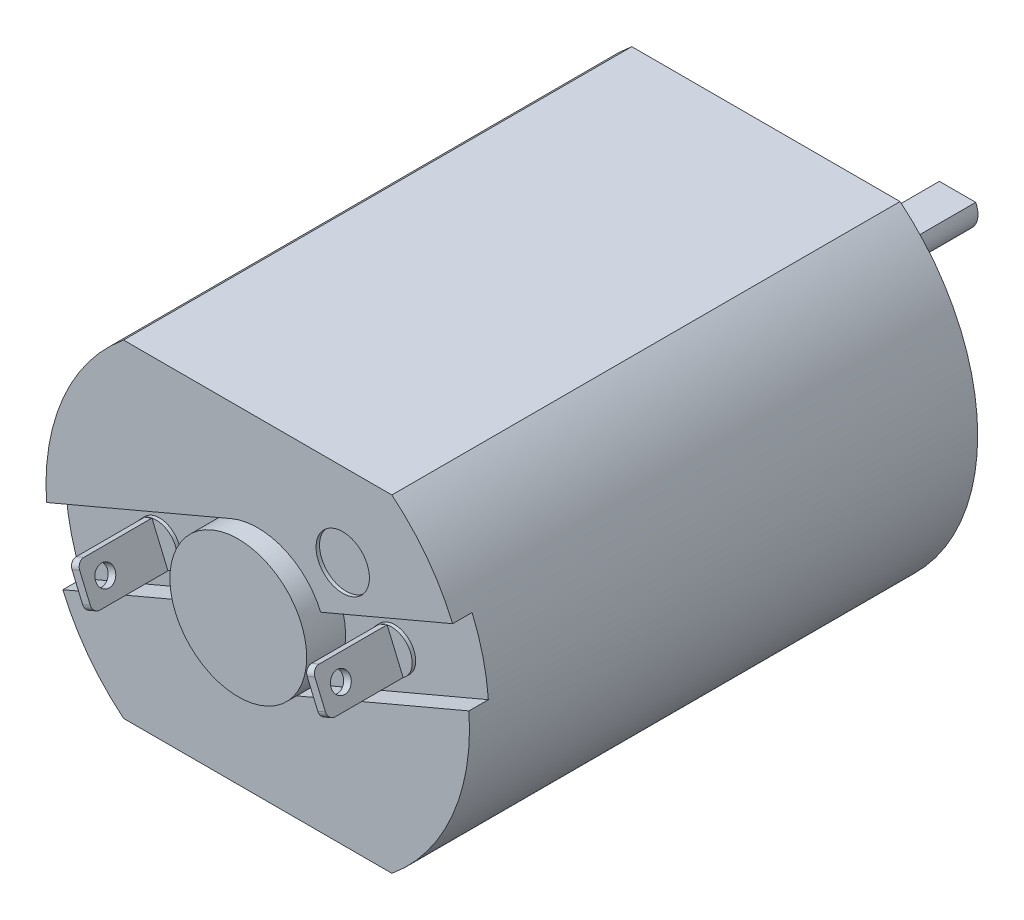
SolidWorks part; units mm, degrees
ref_plane "Front" through (0, 0, 0) normal (0, 0, 1) x (1, 0, 0)
ref_plane "Top" through (0, 0, 0) normal (0, 1, 0) x (1, 0, 0)
ref_plane "Right" through (0, 0, 0) normal (1, 0, 0) x (0, 0, -1)
sketch "Sketch1" plane through (0, 0, 0) normal (0, 0, 1) x (1, 0, 0)
  line L0 (-4.9075, 5.9944) -> (4.9075, 5.9944)
  line L1 (-4.9075, -5.9944) -> (4.9075, -5.9944)
  arc A0 (-4.9075, 5.9944) -> (-4.9075, -5.9944) centre (0, 0) ccw
  arc A1 (4.9075, -5.9944) -> (4.9075, 5.9944) centre (0, 0) ccw
  dimension "D1" = 15.494
  dimension "D2" = 5.9944
  dimension "D3" = 11.9888
extrude "Extrude1" add sketch "Sketch1" along normal blind 18.5928
sketch "Sketch2" plane through (0, 0, 0) normal (0, 0, -1) x (-1, 0, 0)
  circle A0 centre (0, 0) radius 2.3495
  dimension "D1" = 4.699
extrude "Extrude2" add sketch "Sketch2" along normal blind 1.524
sketch "Sketch3" plane through (0, 0, -1.524) normal (0, 0, -1) x (-1, 0, 0)
  circle A0 centre (0, 0) radius 0.748
  dimension "D1" = 1.4961
extrude "Extrude3" add sketch "Sketch3" along normal blind 5.4864
sketch "Sketch4" plane through (0, 0, 18.5928) normal (0, 0, 1) x (1, 0, 0)
  circle A0 centre (0, 0) radius 2.5019
  dimension "D1" = 5.0038
extrude "Extrude4" add sketch "Sketch4" along normal blind 0.7112
sketch "Sketch6" plane through (0, 0, 0) normal (0, 0, -1) x (-1, 0, 0)
  line L0 (0, 0) -> (-5.4518, -3.1476) construction
  line L1 (0, 0) -> (6.0345, 3.484) construction
  line L2 (0, 0) -> (6.2404, 0) construction
  line L3 (0, 0) -> (-6.1628, 0) construction
  circle A0 centre (0, 0) radius 2.3495 construction
  circle A1 centre (4.3334, 2.5019) radius 0.8066
  circle A2 centre (0, 0) radius 5.0038 construction
  circle A3 centre (-4.3334, -2.5019) radius 0.8001
  dimension "D1" = 1.6132
  dimension "D2" = 1.6002
  dimension "D7" = 10.0076
  dimension "D5" = 30
  dimension "D6" = 30
extrude "Cut-Extrude1" cut sketch "Sketch6" against normal blind 2
sketch "Sketch8" plane through (0, 0, 18.5928) normal (0, 0, 1) x (1, 0, 0)
  line L0 (2.303, 0.9776) -> (7.2224, 3.0657)
  line L1 (8.2, 0.7627) -> (0.9776, -2.303)
  line L3 (7.2224, 3.0657) -> (8.2, 0.7627)
  line L4 (0, 0) -> (4.7854, 0) construction
  circle A0 centre (0, 0) radius 2.5019 construction
  arc A3 (0.9776, -2.303) -> (2.303, 0.9776) centre (0, 0) ccw
  dimension "D1" = 23
  dimension "D2" = 7.8462
extrude "Cut-Extrude2" cut sketch "Sketch8" against normal blind 0.7112
sketch "Sketch9" plane through (0, 0, 18.5928) normal (0, 0, 1) x (1, 0, 0)
  line L0 (-2.303, -0.9776) -> (-8.4179, -3.5732)
  line L1 (-8.4179, -3.5732) -> (-9.3954, -1.2702)
  line L2 (-9.3954, -1.2702) -> (-0.9776, 2.303)
  line L5 (0.9776, -2.303) -> (7.7266, 0.5618) construction
  circle A0 centre (0, 0) radius 2.5019 construction
  arc A1 (-0.9776, 2.303) -> (-2.303, -0.9776) centre (0, 0) ccw
  dimension "D1" = 9.1448
extrude "Cut-Extrude3" cut sketch "Sketch9" against normal blind 0.7112
sketch "Sketch10" plane through (0, 0, 17.8816) normal (0, 0, 1) x (1, 0, 0)
  line L0 (-4.7354, 0.1698) -> (-4.1499, -1.2096)
  line L1 (-4.1499, -1.2096) -> (-3.8693, -1.0905)
  line L2 (-3.8693, -1.0905) -> (-4.4548, 0.2889)
  line L3 (-4.4548, 0.2889) -> (-4.7354, 0.1698)
  line L4 (3.8693, 1.0905) -> (4.1499, 1.2096)
  line L5 (4.1499, 1.2096) -> (4.7354, -0.1698)
  line L6 (4.7354, -0.1698) -> (4.4548, -0.2889)
  line L7 (4.4548, -0.2889) -> (3.8693, 1.0905)
  line L8 (-0.9776, 2.303) -> (-7.7266, -0.5618) construction
  line L9 (-7.1312, -3.027) -> (-2.303, -0.9776) construction
  line L10 (0.9776, -2.303) -> (7.7266, 0.5618) construction
  line L11 (7.1312, 3.027) -> (2.303, 0.9776) construction
  dimension "D1" = 3.9878
  dimension "D2" = 0.3048
  dimension "D3" = 0.508
  dimension "D4" = 1.4986
  dimension "D5" = 3.9878
  dimension "D6" = 0.3048
  dimension "D7" = 0.508
  dimension "D8" = 1.4986
extrude "Extrude5" add sketch "Sketch10" along normal blind 2.8702
fillet "Fillet1" radius 0.254 4 edges at (4.5951, -0.2294, 20.7518) (4.0096, 1.1501, 20.7518) (-4.0096, -1.1501, 20.7518) (-4.5951, 0.2294, 20.7518)
sketch "Sketch11" plane through (-3.9514, -1.6773, 0) normal (-0.9205, -0.3907, 0) x (0, 0, 1)
  line L0 (20.7518, 1.7526) -> (20.7518, 0.762) construction
  line L1 (20.4978, 0.508) -> (17.8816, 0.508) construction
  circle A0 centre (20.0014, 1.27) radius 0.3556
  dimension "D1" = 0.7112
  dimension "D2" = 0.7504
  dimension "D3" = 0.762
extrude "Cut-Extrude4" cut sketch "Sketch11" against normal blind 0.381
sketch "Sketch12" plane through (3.9514, 1.6773, 0) normal (0.9205, 0.3907, 0) x (0, 0, -1)
  line L0 (-20.4978, -2.0066) -> (-17.8816, -2.0066) construction
  line L2 (-20.7518, -1.7526) -> (-20.7518, -0.762) construction
  circle A0 centre (-19.9898, -1.2446) radius 0.3556
  dimension "D1" = 0.7112
  dimension "D2" = 0.762
  dimension "D3" = 0.762
extrude "Cut-Extrude5" cut sketch "Sketch12" against normal blind 0.381
sketch "Sketch13" plane through (0, 0, 17.8816) normal (0, 0, 1) x (1, 0, 0)
  circle A0 centre (4.3023, 0.4604) radius 0.7646
  circle A2 centre (-4.3023, -0.4604) radius 0.7646
extrude "Extrude6" add sketch "Sketch13" along normal blind 0.127
sketch "Sketch14" plane through (0, 0, 18.5928) normal (0, 0, 1) x (1, 0, 0)
  circle A0 centre (3.1095, 2.9554) radius 0.9764
extrude "Extrude7" cut sketch "Sketch14" against normal blind 0.127
sketch "Sketch15" plane through (0, 0, -7.0104) normal (0, 0, -1) x (-1, 0, 0)
  line L0 (-0.6648, 0.3429) -> (0.6648, 0.3429)
  circle A0 centre (0, 0) radius 0.748 construction
  arc A1 (0.6648, 0.3429) -> (-0.6648, 0.3429) centre (0, 0) ccw
  dimension "D1" = 0.3429
extrude "Extrude8" cut sketch "Sketch15" against normal blind 5.207
